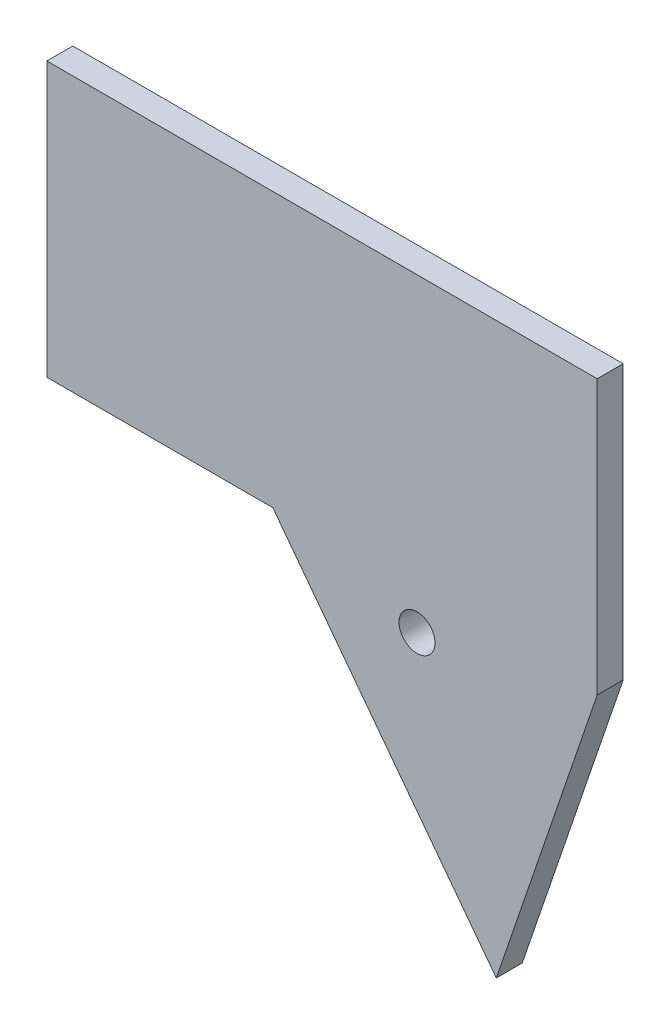
SolidWorks part; units mm, degrees
ref_plane "Front Plane" through (0, 0, 0) normal (0, 0, 1) x (1, 0, 0)
ref_plane "Top Plane" through (0, 0, 0) normal (0, 1, 0) x (1, 0, 0)
ref_plane "Right Plane" through (0, 0, 0) normal (1, 0, 0) x (0, 0, -1)
sketch "Sketch1" plane through (0, 0, 0) normal (0, 0, 1) x (1, 0, 0)
  line L1 (-16, 19) -> (60.3546, 19)
  line L2 (-16, 19) -> (-16, -19)
  line L3 (-16, -19) -> (60.3546, -19)
  line L4 (60.3546, 19) -> (60.3546, -19)
  circle A0 centre (0, 0) radius 4.55
  circle A1 centre (0, 0) radius 7.55 construction
  point P8 (-16, 0)
  dimension "D1" = 9.1
  dimension "D2" = 3
  dimension "D3" = 16
  dimension "D4" = 38
extrude "Boss-Extrude1" add sketch "Sketch1" along normal blind 3
sketch "Sketch2" plane through (0, 0, 3) normal (0, 0, -1) x (-1, 0, 0)
  line L4 (16, -19) -> (16, 19)
  line L5 (16, 19) -> (-60.3546, 19)
  line L6 (-60.3546, 19) -> (-60.3546, -19)
  line L7 (-60.3546, -19) -> (16, -19)
  line L8 (16, -19) -> (16, 19)
  line L9 (16, 19) -> (-60.3546, 19)
  line L10 (-60.3546, 19) -> (-60.3546, -19)
  line L11 (-60.3546, -19) -> (16, -19)
  dimension "D1" = 0
extrude "Boss-Extrude2" add sketch "Sketch2" against normal blind 0.6
sketch "Sketch3" plane through (0, 0, 3) normal (0, 0, -1) x (-1, 0, 0)
  circle A0 centre (0, 0) radius 3.5
  dimension "D1" = 7
extrude "Cut-Extrude1" cut sketch "Sketch3" against normal blind 0.4
sketch "Sketch4" plane through (0, 0, 0) normal (0, 0, -1) x (-1, 0, 0)
  line L0 (-15.3546, -19) -> (-46.3546, -60)
  line L1 (16, -19) -> (-60.3546, -19) construction
  line L2 (-46.3546, -60) -> (-60.3546, -19)
  line L3 (-60.3546, -19) -> (-60.3546, 19) construction
  line L4 (-60.3546, -19) -> (-15.3546, -19)
  circle A0 centre (-35.3546, -24) radius 2.5
  point P7 (-29.2314, -62.0535)
  point P11 (-29.2314, -60.9955)
  dimension "D5" = 5
  dimension "D1" = 45
  dimension "D2" = 5
  dimension "D3" = 25
  dimension "D4" = 14
  dimension "D6" = 41
extrude "Boss-Extrude3" add sketch "Sketch4" against normal up to surface (3.6 mm away) up to face at (22.1773, 0, 3.6)
